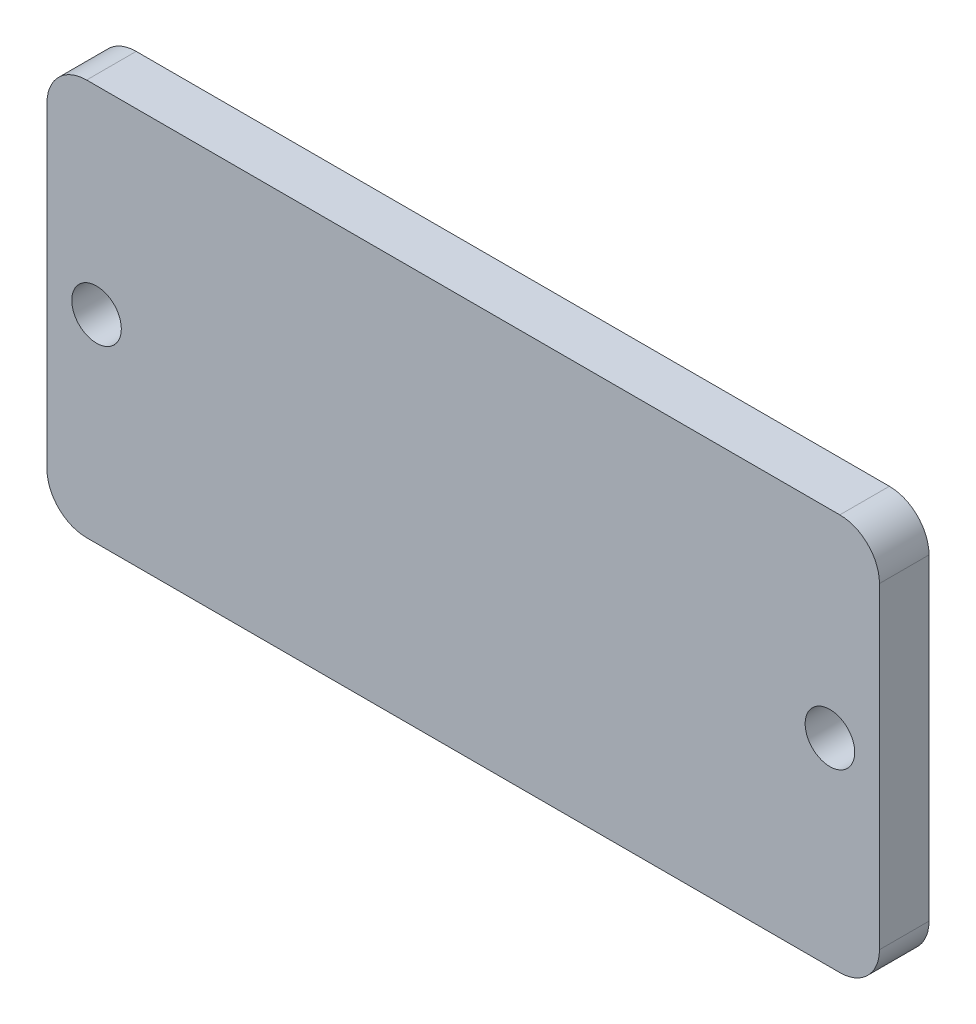
SolidWorks part; units mm, degrees
ref_plane "Front Plane" through (0, 0, 0) normal (0, 0, 1) x (1, 0, 0)
ref_plane "Top Plane" through (0, 0, 0) normal (0, 1, 0) x (1, 0, 0)
ref_plane "Right Plane" through (0, 0, 0) normal (1, 0, 0) x (0, 0, -1)
sketch "Sketch1" plane through (0, 0, 0) normal (0, 0, 1) x (1, 0, 0)
  line L0 (-26.67, 0) -> (26.67, 0) construction
  line L1 (24.13, -12.7) -> (-24.13, -12.7)
  line L2 (26.67, -10.16) -> (26.67, 10.16)
  line L3 (24.13, 12.7) -> (-24.13, 12.7)
  line L4 (-26.67, -10.16) -> (-26.67, 10.16)
  line L5 (0, 12.7) -> (0, -12.7) construction
  circle A0 centre (-23.495, 0) radius 1.5875
  circle A1 centre (23.495, 0) radius 1.5875
  arc A2 (24.13, -12.7) -> (26.67, -10.16) centre (24.13, -10.16) ccw
  arc A3 (26.67, 10.16) -> (24.13, 12.7) centre (24.13, 10.16) ccw
  arc A4 (-24.13, 12.7) -> (-26.67, 10.16) centre (-24.13, 10.16) ccw
  arc A5 (-24.13, -12.7) -> (-26.67, -10.16) centre (-24.13, -10.16) cw
  point P15 (26.67, -12.7)
  point P20 (-26.67, 12.7)
  point P23 (-26.67, -12.7)
  dimension "D3" = 3.175
  dimension "D5" = 2.54
  dimension "D1" = 53.34
  dimension "D2" = 25.4
  dimension "D4" = 3.175
extrude "Boss-Extrude1" add sketch "Sketch1" along normal blind 3.175
